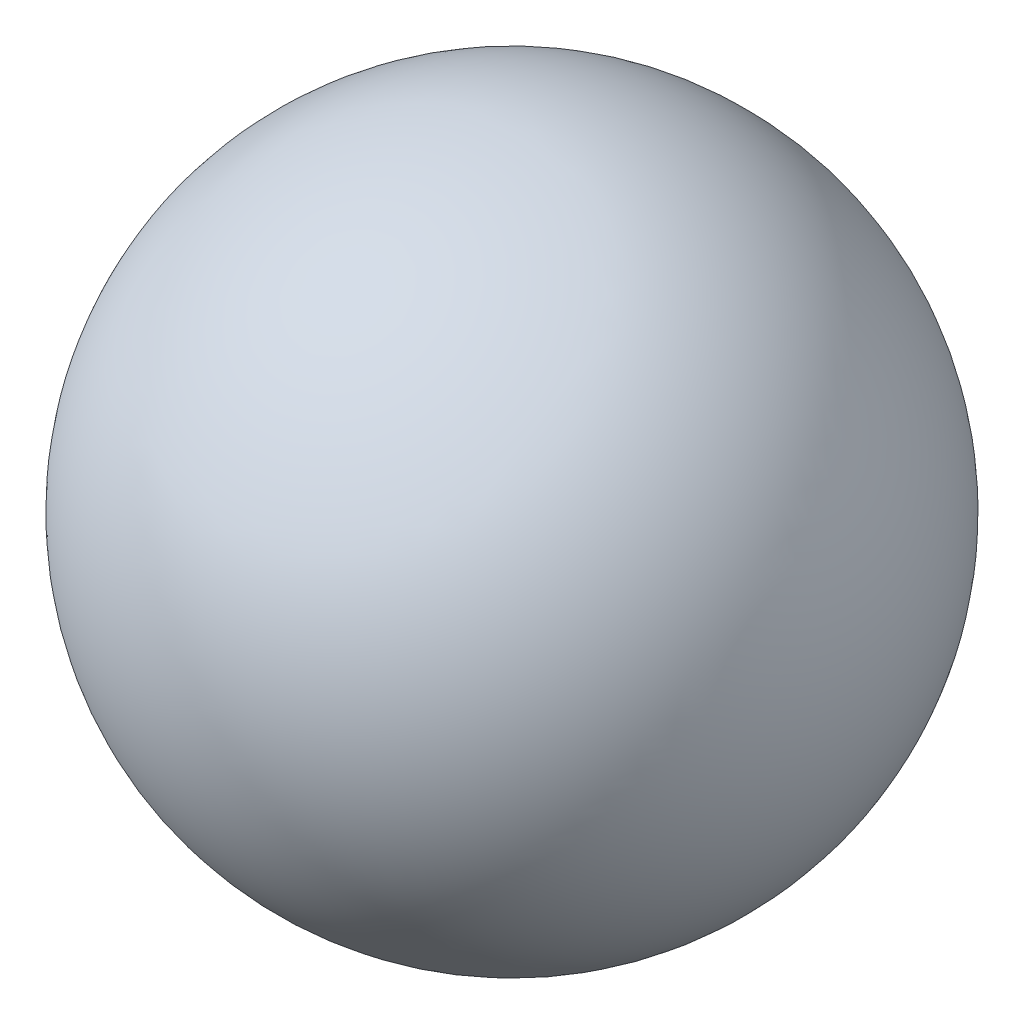
SolidWorks part; units mm, degrees
ref_plane "Front Plane" through (0, 0, 0) normal (0, 0, 1) x (1, 0, 0)
ref_plane "Top Plane" through (0, 0, 0) normal (0, 1, 0) x (1, 0, 0)
ref_plane "Right Plane" through (0, 0, 0) normal (1, 0, 0) x (0, 0, -1)
sketch "Sketch1" plane through (0, 0, 0) normal (0, 0, 1) x (1, 0, 0)
  line L0 (-13.288, 0) -> (14.7727, 0) construction
  line L1 (55, 0) -> (-55, 0) construction
  line L2 (0.75, 0) -> (-0.75, 0)
  arc A0 (-0.75, 0) -> (0.75, 0) centre (0, 0) ccw
  dimension "D1" = 1.5
revolve "Revolve1" add sketch "Sketch1" angle 360 about L0
